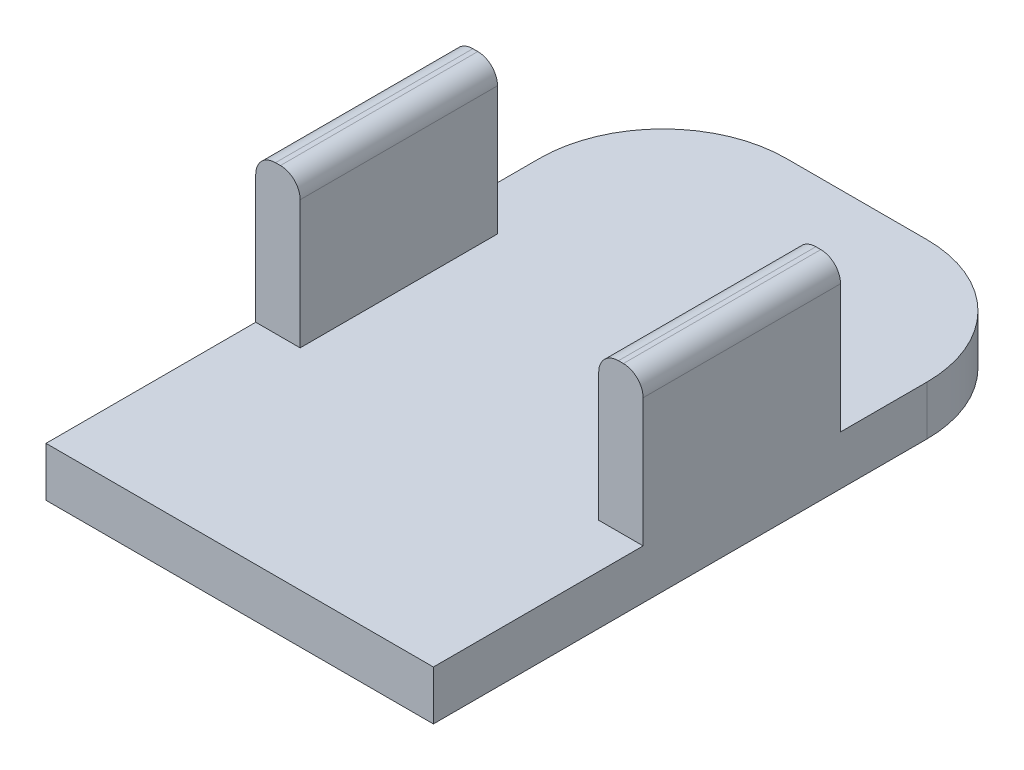
SolidWorks part; units mm, degrees
ref_plane "Front Plane" through (0, 0, 0) normal (0, 0, 1) x (1, 0, 0)
ref_plane "Top Plane" through (0, 0, 0) normal (0, 1, 0) x (1, 0, 0)
ref_plane "Right Plane" through (0, 0, 0) normal (1, 0, 0) x (0, 0, -1)
sketch "Sketch1" plane through (0, 0, 0) normal (0, 1, 0) x (1, 0, 0)
  line L0 (-19.939, -6.35) -> (19.939, -6.35) construction
  line L1 (-7.239, 31.75) -> (7.239, 31.75)
  line L2 (-19.939, 19.05) -> (-19.939, -31.75)
  line L3 (-19.939, -31.75) -> (19.939, -31.75)
  line L4 (19.939, 19.05) -> (19.939, -31.75)
  line L5 (-19.939, 31.75) -> (19.939, -31.75) construction
  line L6 (-19.939, -31.75) -> (19.939, 31.75) construction
  line L7 (-19.939, 3.81) -> (-17.78, 3.81)
  line L8 (-17.78, 3.81) -> (-17.78, -16.51)
  line L9 (-17.78, -16.51) -> (-19.939, -16.51)
  line L10 (0, 31.75) -> (0, -31.75) construction
  line L11 (17.78, -16.51) -> (19.939, -16.51)
  line L12 (19.939, 3.81) -> (17.78, 3.81)
  line L13 (17.78, 3.81) -> (17.78, -16.51)
  line L15 (-7.239, 31.75) -> (7.239, 31.75)
  line L16 (-7.239, 31.75) -> (-7.239, 1.27)
  line L17 (-7.239, 1.27) -> (7.239, 1.27)
  line L18 (7.239, 31.75) -> (7.239, 1.27)
  line L19 (-7.239, 31.75) -> (7.239, 1.27) construction
  line L20 (-7.239, 1.27) -> (7.239, 31.75) construction
  arc A0 (19.939, 19.05) -> (7.239, 31.75) centre (7.239, 19.05) ccw
  arc A1 (-7.239, 31.75) -> (-19.939, 19.05) centre (-7.239, 19.05) ccw
  point P1 (0, 0)
  point P18 (-17.78, -6.35)
  point P25 (0, 16.51)
  dimension "D5" = 12.7
  dimension "D1" = 63.5
  dimension "D2" = 39.878
  dimension "D3" = 17.78
  dimension "D4" = 20.32
  dimension "D6" = 30.48
extrude "Boss-Extrude2" add sketch "Sketch1" along normal blind 5.08 separate body contours L2 A1 L1 A0 L4 L3
sketch "Sketch3" plane through (0, 5.08, 0) normal (0, 1, 0) x (1, 0, 0)
  line L0 (-19.939, 19.05) -> (-19.939, -31.75) construction
  line L2 (-19.939, 10.16) -> (-15.367, 10.16)
  line L3 (-19.939, 10.16) -> (-19.939, -10.16)
  line L4 (-19.939, -10.16) -> (-15.367, -10.16)
  line L5 (-15.367, 10.16) -> (-15.367, -10.16)
  line L6 (0, 31.75) -> (0, -31.75) construction
  line L7 (-7.239, 31.75) -> (7.239, 31.75) construction
  line L8 (-19.939, -31.75) -> (19.939, -31.75) construction
  line L9 (19.939, -10.16) -> (15.367, -10.16)
  line L10 (15.367, 10.16) -> (15.367, -10.16)
  line L11 (19.939, 10.16) -> (15.367, 10.16)
  line L12 (19.939, 10.16) -> (19.939, -10.16)
  line L13 (-21.9329, 0) -> (21.9329, 0) construction
  point P16 (-15.367, 0)
  dimension "D1" = 4.572
  dimension "D2" = 20.32
extrude "Boss-Extrude3" add sketch "Sketch3" along normal blind 15.24
fillet "Fillet1" radius 2.032 4 edges at (15.367, 20.32, 0) (-15.367, 20.32, 0) (19.939, 20.32, 0) (-19.939, 20.32, 0)
sketch "Sketch4" plane through (0, 0, 0) normal (0, -1, 0) x (1, 0, 0)
  line L0 (-7.239, -31.75) -> (7.239, -31.75) construction
  line L1 (-2.032, -31.75) -> (0, -31.75)
  line L2 (-2.032, -31.75) -> (-2.032, -26.67)
  line L3 (-2.032, -26.67) -> (0, -26.67)
  line L4 (0, -31.75) -> (0, -26.67)
  line L5 (0, -2.794) -> (0, 2.794) construction
  point P5 (0, 0)
  point P6 (0, 0)
  point P7 (0, 0)
  point P10 (0, 0)
  dimension "D1" = 2.032
  dimension "D2" = 5.08
extrude "Tilt servo connection" add sketch "Sketch4" along normal blind 12.7
sketch "Sketch5" plane through (0, 0, 0) normal (1, 0, 0) x (0, 0, -1)
  line L0 (29.21, 0) -> (29.21, -7.62) construction
  line L3 (21.9329, 0) -> (-21.9329, 0) construction
  line L4 (29.21, -12.7) -> (29.21, -7.62) construction
  line L5 (31.75, -12.7) -> (26.67, -12.7) construction
  circle A0 centre (29.21, -7.62) radius 0.889
  point P4 (32.385, -13.4593)
  dimension "D1" = 1.778
  dimension "D2" = 5.08
extrude "Cut-Extrude1" cut sketch "Sketch5" against normal blind 12.7
chamfer "Chamfer1" distance 5.08 angle 20 2 edges at (-1.016, -12.7, -31.75) (-1.016, -12.7, -26.67)
